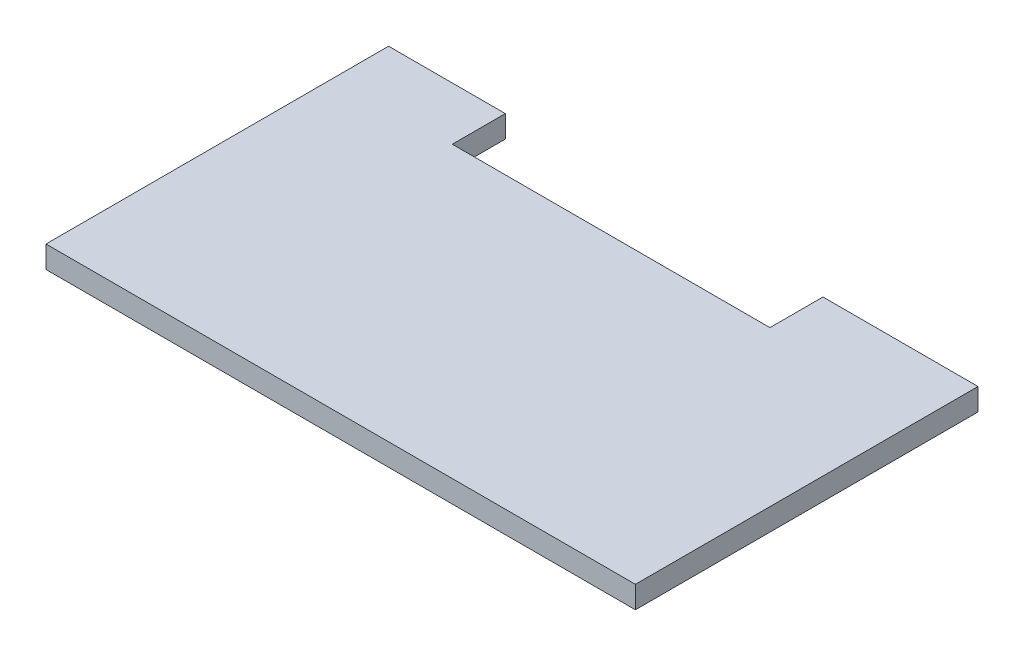
SolidWorks part; units mm, degrees
ref_plane "Front Plane" through (0, 0, 0) normal (0, 0, 1) x (1, 0, 0)
ref_plane "Top Plane" through (0, 0, 0) normal (0, 1, 0) x (1, 0, 0)
ref_plane "Right Plane" through (0, 0, 0) normal (1, 0, 0) x (0, 0, -1)
sketch "Sketch1" plane through (0, 0, 0) normal (0, 1, 0) x (1, 0, 0)
  line L0 (15.8432, 46.5) -> (15.8432, 39.3)
  line L1 (0, 0) -> (80, 0)
  line L2 (0, 0) -> (0, 46.5)
  line L3 (0, 46.5) -> (15.8432, 46.5)
  line L4 (80, 0) -> (80, 46.5)
  line L5 (15.8432, 39.3) -> (58.9568, 39.3)
  line L6 (58.9568, 39.3) -> (58.9568, 46.5)
  line L7 (80, 39.3) -> (0, 39.3) construction
  line L9 (58.9568, 46.5) -> (80, 46.5)
sketch "Sketch2" plane through (0, 0, 0) normal (0, 0, 1) x (1, 0, 0)
  line L1 (0, 0) -> (80, 0)
  line L2 (0, 0) -> (0, -3)
  line L3 (0, -3) -> (80, -3)
  line L4 (80, 0) -> (80, -3)
extrude "Boss-Extrude1" add sketch "Sketch1" against normal up to vertex (3 mm away) up to point (0, -3, 0)
